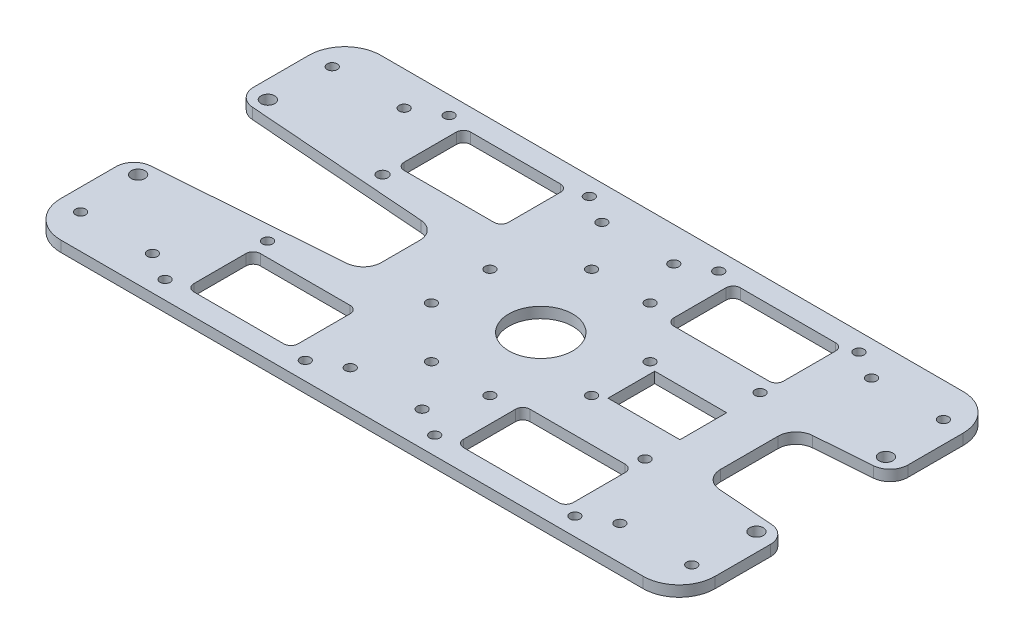
SolidWorks part; units mm, degrees
ref_plane "Front Plane" through (0, 0, 0) normal (0, 0, 1) x (1, 0, 0)
ref_plane "Top Plane" through (0, 0, 0) normal (0, 1, 0) x (1, 0, 0)
ref_plane "Right Plane" through (0, 0, 0) normal (1, 0, 0) x (0, 0, -1)
sketch "Sketch1" plane through (0, 0, 0) normal (0, 1, 0) x (1, 0, 0)
  line L0 (0, 0) -> (0, 14.6791) construction
  line L9 (-33, 20) -> (-58, 20)
  line L10 (-31, 36.5) -> (-31, 22)
  line L11 (-58, 38.5) -> (-33, 38.5)
  line L24 (78.3739, -14.153) -> (62.6261, -12.972)
  line L25 (58, -7.986) -> (58, 7.986)
  line L26 (62.6261, 12.972) -> (78.3739, 14.153)
  line L27 (83, 19.139) -> (83, 34.5)
  line L28 (73, 44.5) -> (-89, 44.5)
  line L29 (-99, 34.5) -> (-99, 19.139)
  line L30 (-94.3739, 14.153) -> (-43.6261, 10.347)
  line L31 (-39, 5.361) -> (-39, -5.361)
  line L32 (-43.6261, -10.347) -> (-94.3739, -14.153)
  line L33 (-99, -19.139) -> (-99, -34.5)
  line L34 (-89, -44.5) -> (73, -44.5)
  line L35 (83, -34.5) -> (83, -19.139)
  line L36 (-60, 22) -> (-60, 36.5)
  line L45 (45.205, -6.5) -> (25.205, -6.5)
  line L46 (45.205, 6.5) -> (45.205, -6.5)
  line L47 (25.205, 6.5) -> (45.205, 6.5)
  line L48 (25.205, -6.5) -> (25.205, 6.5)
  line L49 (45.5, 36.5) -> (45.5, 22)
  line L50 (17, 38.5) -> (43.5, 38.5)
  line L51 (43.5, 20) -> (17, 20)
  line L52 (15, 22) -> (15, 36.5)
  line L61 (43.5, -38.5) -> (17, -38.5)
  line L62 (45.5, -22) -> (45.5, -36.5)
  line L63 (17, -20) -> (43.5, -20)
  line L64 (15, -36.5) -> (15, -22)
  line L65 (-31, -22) -> (-31, -36.5)
  line L66 (-58, -20) -> (-33, -20)
  line L67 (-33, -38.5) -> (-58, -38.5)
  line L68 (-60, -36.5) -> (-60, -22)
  circle A0 centre (0, 0) radius 8.9
  arc A24 (83, -19.139) -> (78.3739, -14.153) centre (78, -19.139) ccw
  arc A25 (58, -7.986) -> (62.6261, -12.972) centre (63, -7.986) ccw
  arc A26 (62.6261, 12.972) -> (58, 7.986) centre (63, 7.986) ccw
  arc A27 (78.3739, 14.153) -> (83, 19.139) centre (78, 19.139) ccw
  arc A28 (83, 34.5) -> (73, 44.5) centre (73, 34.5) ccw
  arc A29 (-89, 44.5) -> (-99, 34.5) centre (-89, 34.5) ccw
  arc A30 (-99, 19.139) -> (-94.3739, 14.153) centre (-94, 19.139) ccw
  arc A31 (-39, 5.361) -> (-43.6261, 10.347) centre (-44, 5.361) ccw
  arc A32 (-43.6261, -10.347) -> (-39, -5.361) centre (-44, -5.361) ccw
  arc A33 (-94.3739, -14.153) -> (-99, -19.139) centre (-94, -19.139) ccw
  arc A34 (-99, -34.5) -> (-89, -44.5) centre (-89, -34.5) ccw
  arc A35 (73, -44.5) -> (83, -34.5) centre (73, -34.5) ccw
  circle A66 centre (78, -18) radius 1.9
  circle A67 centre (77, -35) radius 1.4
  circle A68 centre (57, -35) radius 1.4
  circle A69 centre (49, -39.5) radius 1.4
  circle A70 centre (45, -16) radius 1.4
  circle A72 centre (22.2739, -8.1317) radius 1.4
  circle A74 centre (22.2739, 8.1317) radius 1.4
  circle A77 centre (10, -39.5) radius 1.4
  circle A78 centre (2, -35) radius 1.4
  circle A79 centre (8.1317, -22.2739) radius 1.4
  circle A80 centre (-8.1317, -22.2739) radius 1.4
  circle A81 centre (-18, -35) radius 1.4
  circle A82 centre (-26, -39.5) radius 1.4
  circle A84 centre (-22.2739, -8.1317) radius 1.4
  circle A85 centre (-22.2739, 8.1317) radius 1.4
  circle A87 centre (-8.1317, 22.2739) radius 1.4
  circle A88 centre (8.1317, 22.2739) radius 1.4
  circle A89 centre (45, 16) radius 1.4
  circle A90 centre (78, 18) radius 1.9
  circle A91 centre (77, 35) radius 1.4
  circle A92 centre (57, 35) radius 1.4
  circle A93 centre (49, 39.5) radius 1.4
  circle A94 centre (10, 39.5) radius 1.4
  circle A95 centre (2, 35) radius 1.4
  circle A96 centre (-18, 35) radius 1.4
  circle A97 centre (-26, 39.5) radius 1.4
  circle A98 centre (-60, 16) radius 1.5
  circle A99 centre (-60, -16) radius 1.4
  circle A100 centre (-65, -39.5) radius 1.4
  circle A101 centre (-73, -35) radius 1.4
  circle A102 centre (-93, -35) radius 1.4
  circle A103 centre (-94, -18) radius 1.9
  circle A104 centre (-94, 18.0964) radius 1.9
  circle A105 centre (-93, 35) radius 1.4
  circle A106 centre (-73, 35) radius 1.4
  circle A107 centre (-65, 39.5) radius 1.4
  arc A113 (-33, 20) -> (-31, 22) centre (-33, 22) ccw
  arc A114 (-31, 36.5) -> (-33, 38.5) centre (-33, 36.5) ccw
  arc A115 (-58, 38.5) -> (-60, 36.5) centre (-58, 36.5) ccw
  arc A116 (-60, 22) -> (-58, 20) centre (-58, 22) ccw
  arc A121 (43.5, 20) -> (45.5, 22) centre (43.5, 22) ccw
  arc A122 (45.5, 36.5) -> (43.5, 38.5) centre (43.5, 36.5) ccw
  arc A123 (15, 22) -> (17, 20) centre (17, 22) ccw
  arc A124 (17, 38.5) -> (15, 36.5) centre (17, 36.5) ccw
  arc A133 (43.5, -38.5) -> (45.5, -36.5) centre (43.5, -36.5) ccw
  arc A134 (45.5, -22) -> (43.5, -20) centre (43.5, -22) ccw
  arc A135 (17, -20) -> (15, -22) centre (17, -22) ccw
  arc A136 (15, -36.5) -> (17, -38.5) centre (17, -36.5) ccw
  arc A137 (-33, -38.5) -> (-31, -36.5) centre (-33, -36.5) ccw
  arc A138 (-31, -22) -> (-33, -20) centre (-33, -22) ccw
  arc A139 (-60, -36.5) -> (-58, -38.5) centre (-58, -36.5) ccw
  arc A140 (-58, -20) -> (-60, -22) centre (-58, -22) ccw
  dimension "D1" = 17.8
  dimension "D4" = 3.8
  dimension "D2" = 2.8
  dimension "D3" = 2.8
  dimension "D5" = 20
extrude "Boss-Extrude1" add sketch "Sketch1" along normal blind 3
